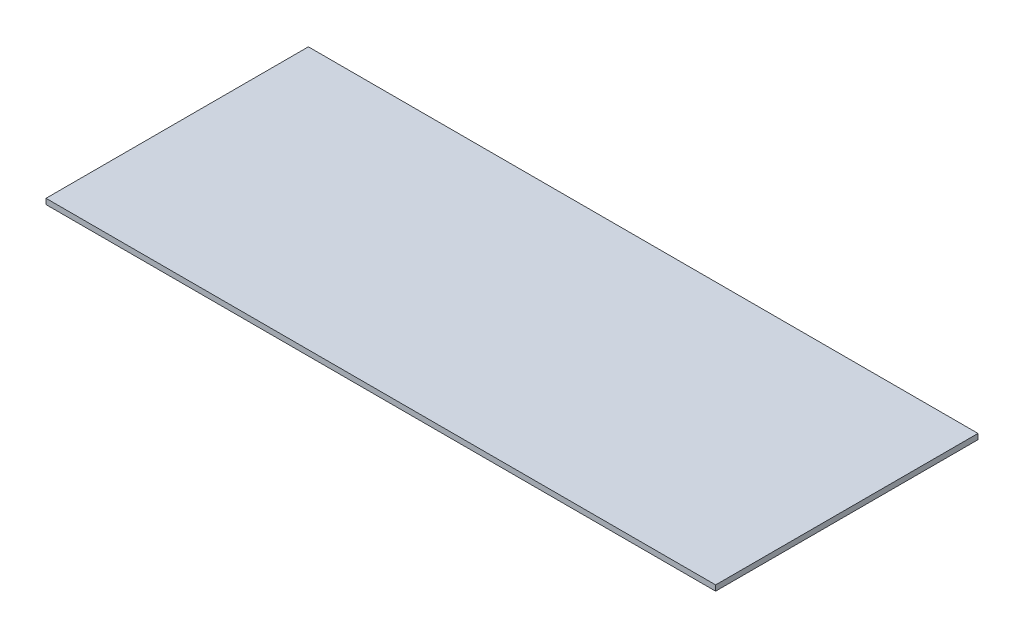
SolidWorks part; units mm, degrees
ref_plane "Front Plane" through (0, 0, 0) normal (0, 0, 1) x (1, 0, 0)
ref_plane "Top Plane" through (0, 0, 0) normal (0, 1, 0) x (1, 0, 0)
ref_plane "Right Plane" through (0, 0, 0) normal (1, 0, 0) x (0, 0, -1)
sketch "Sketch2" plane through (0, 0, 0) normal (0, 1, 0) x (1, 0, 0)
  line L1 (-122.5, 48) -> (122.5, 48)
  line L2 (-122.5, 48) -> (-122.5, -48)
  line L3 (-122.5, -48) -> (122.5, -48)
  line L4 (122.5, 48) -> (122.5, -48)
  line L5 (-122.5, 48) -> (122.5, -48) construction
  line L6 (-122.5, -48) -> (122.5, 48) construction
  point P0 (0, 0)
  dimension "D1" = 96
  dimension "D2" = 245
extrude "Boss-Extrude1" add sketch "Sketch2" along normal blind 2
sketch "Sketch3" plane through (0, 2, 0) normal (0, 1, 0) x (1, 0, 0)
  line L4 (-10.5219, 0) -> (182.837, 0) construction
